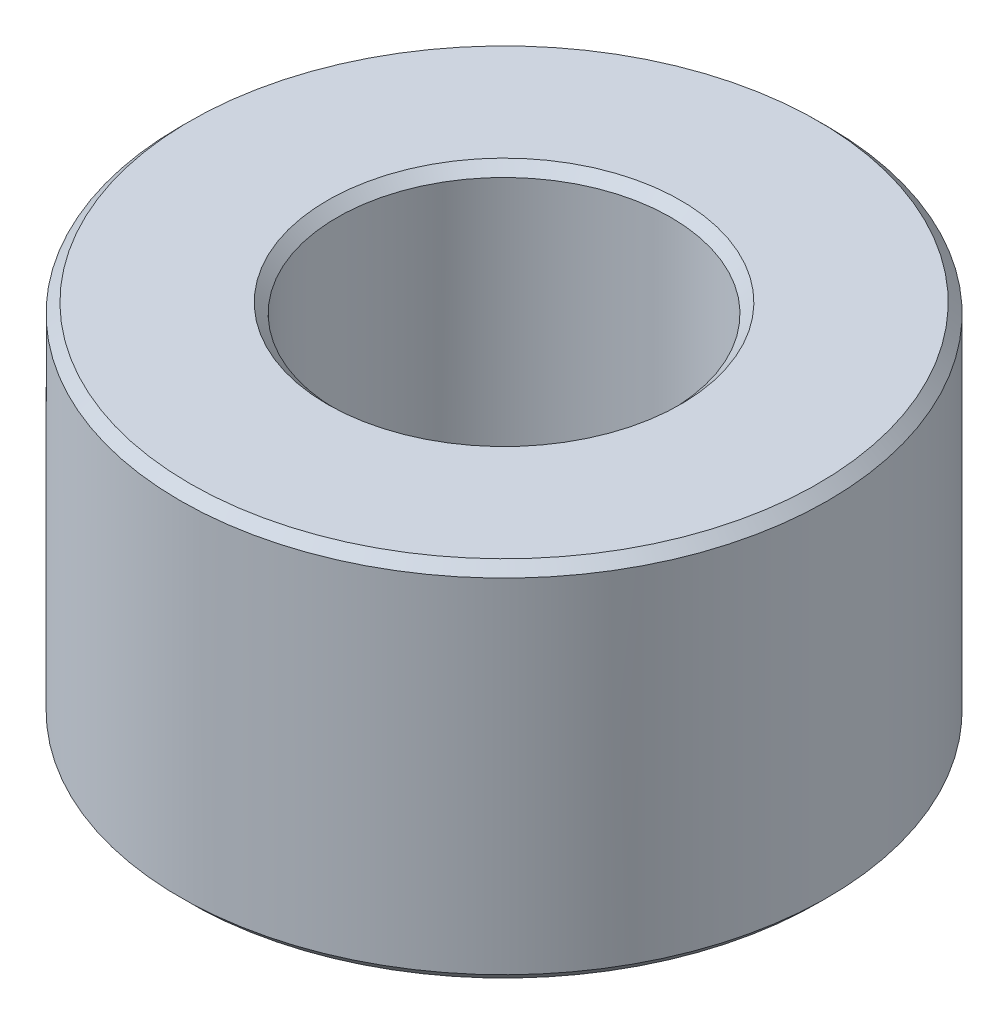
SolidWorks part; units mm, degrees
ref_plane "Front Plane" through (0, 0, 0) normal (0, 0, 1) x (1, 0, 0)
ref_plane "Top Plane" through (0, 0, 0) normal (0, 1, 0) x (1, 0, 0)
ref_plane "Right Plane" through (0, 0, 0) normal (1, 0, 0) x (0, 0, -1)
sketch "Sketch1" plane through (0, 0, 0) normal (0, 1, 0) x (1, 0, 0)
  circle A0 centre (0, 0) radius 16.5
  circle A1 centre (0, 0) radius 8.5
  dimension "D1" = 17
  dimension "D2" = 8
extrude "Boss-Extrude1" add sketch "Sketch1" along normal blind 15.5
sketch "Sketch2" plane through (0, 0, 0) normal (0, -1, 0) x (1, 0, 0)
  circle A0 centre (0, 0) radius 41.6346
  circle A1 centre (0, 0) radius 2.15
  circle M2 centre (0, 0) radius 16.5
  circle M3 centre (0, 0) radius 8.5
  dimension "D1" = 4.3
extrude "Boss-Extrude2" add sketch "Sketch2" along normal blind 3 and the other way blind 1 contours A1 M3 | M2 M3 | A0
chamfer "Chamfer2" distance 0.5 angle 45 3 edges at (0, -3, -16.5) (0, 15.5, 8.5) (0, 15.5, 16.5)
chamfer "Chamfer3" distance 2 angle 45 1 edges at (0, 1, -8.5)
